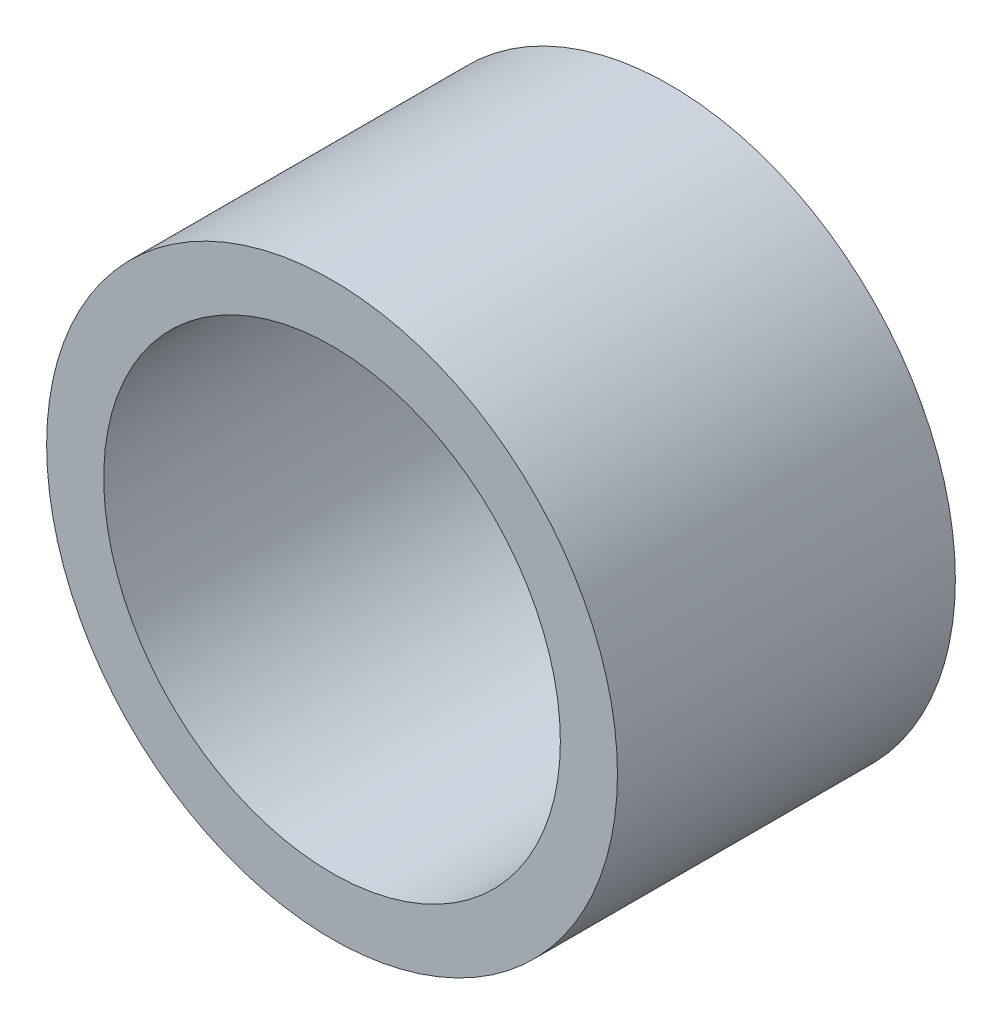
SolidWorks part; units mm, degrees
ref_plane "Front Plane" through (0, 0, 0) normal (0, 0, 1) x (1, 0, 0)
ref_plane "Top Plane" through (0, 0, 0) normal (0, 1, 0) x (1, 0, 0)
ref_plane "Right Plane" through (0, 0, 0) normal (1, 0, 0) x (0, 0, -1)
sketch "Sketch1" plane through (0, 0, 0) normal (0, 0, 1) x (1, 0, 0)
  circle A0 centre (0, 0) radius 3.175
  circle A1 centre (0, 0) radius 3.9688
extrude "Extrude1" add sketch "Sketch1" along normal blind 4.699
